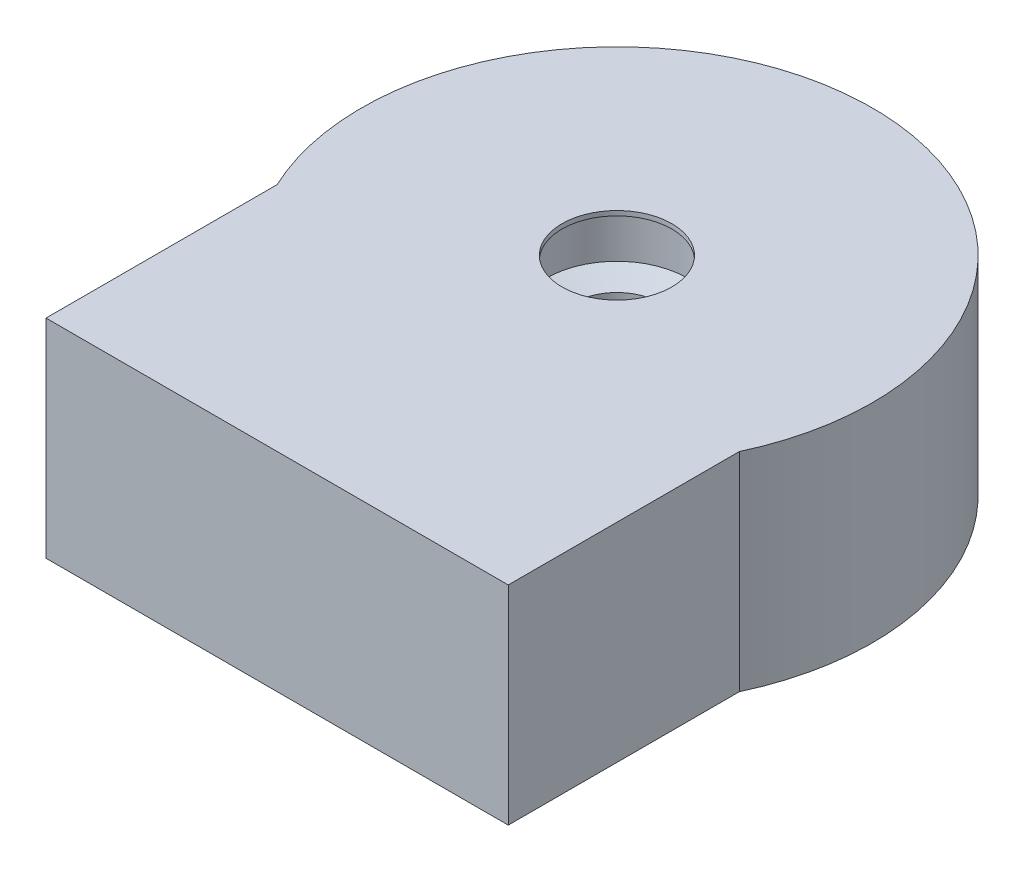
SolidWorks part; units mm, degrees
ref_plane "Front Plane" through (0, 0, 0) normal (0, 0, 1) x (1, 0, 0)
ref_plane "Top Plane" through (0, 0, 0) normal (0, 1, 0) x (1, 0, 0)
ref_plane "Right Plane" through (0, 0, 0) normal (1, 0, 0) x (0, 0, -1)
sketch "Sketch1" plane through (0, 0, 0) normal (0, 0, 1) x (1, 0, 0)
  line L0 (0, 0) -> (0, 2.3075) construction
  line L1 (11.05, 0) -> (2.375, 0)
  line L2 (2.375, 0) -> (2.375, -0.2)
  line L3 (2.375, -0.2) -> (3.05, -0.2)
  line L4 (3.05, -0.2) -> (3.05, -2.3785)
  line L5 (1.85, -2.7) -> (1.85, -6.3)
  line L6 (11.05, -9) -> (11.05, 0)
  line L7 (1.85, -6.3) -> (1.15, -7)
  line L8 (1.15, -7) -> (0, -7)
  line L9 (0, -7) -> (0, -9)
  line L10 (0, -9) -> (11.05, -9)
  line L11 (1.85, -2.7) -> (3.05, -2.3785)
  circle A0 centre (2.34, 2.5593) radius 0.89 construction
  point P9 (1.85, -7)
  dimension "D1" = 1.78
  dimension "D2" = 0.2
  dimension "D3" = 8
  dimension "D4" = 6.1
  dimension "D5" = 4.75
  dimension "D6" = 3.7
  dimension "D7" = 22.1
  dimension "D8" = 2.9
  dimension "D9" = 2
  dimension "D10" = 75
  dimension "D11" = 2.5
  dimension "D12" = 0.7
  dimension "D13" = 0.7
  dimension "D14" = 7
revolve "Revolve1" add sketch "Sketch1" angle 360 about L0
sketch "Sketch2" plane through (0, 0, 0) normal (0, 1, 0) x (1, 0, 0)
  line L0 (-10, -14.7013) -> (-10, -4.7013)
  line L1 (-10, -14.7013) -> (10, -14.7013)
  line L2 (-10, -4.7013) -> (10, -4.7013)
  line L3 (10, -14.7013) -> (10, -4.7013)
  line L4 (-10, -14.7013) -> (10, -4.7013) construction
  line L5 (-10, -4.7013) -> (10, -14.7013) construction
  circle A1 centre (0, 0) radius 11.05 construction
  point P1 (0, -9.7013)
  dimension "D1" = 10
  dimension "D2" = 20
extrude "Boss-Extrude1" add sketch "Sketch2" against normal up to surface (9 mm away) contours L0 L1 L3 L2 up to face at (0, -9, -11.05)
sketch "Sketch3" plane through (0, 0, 0) normal (0, 1, 0) x (1, 0, 0)
  circle A0 centre (-7.1718, -10.9652) radius 1
  circle A1 centre (-3.7718, -10.9652) radius 1
  dimension "D1" = 2
extrude "Cut-Extrude1" [suppressed] cut sketch "Sketch3" against normal up to surface (9 mm away)
